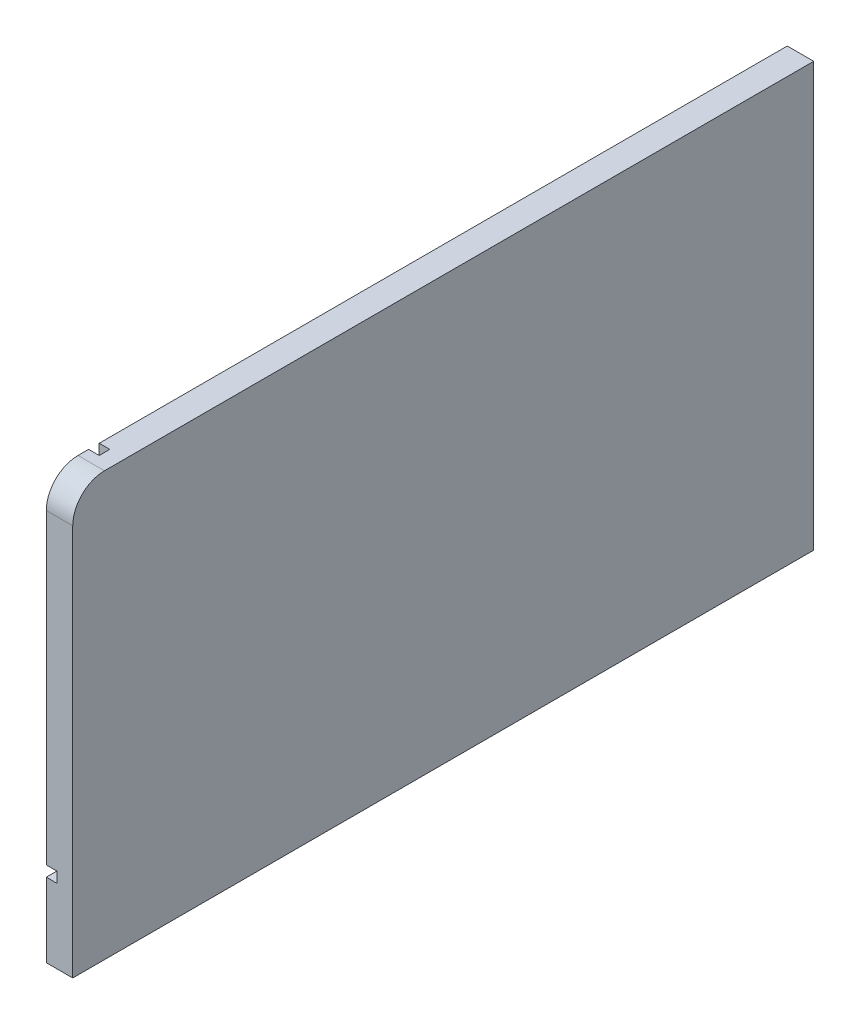
SolidWorks part; units mm, degrees
ref_plane "Front Plane" through (0, 0, 0) normal (0, 0, 1) x (1, 0, 0)
ref_plane "Top Plane" through (0, 0, 0) normal (0, 1, 0) x (1, 0, 0)
ref_plane "Right Plane" through (0, 0, 0) normal (1, 0, 0) x (0, 0, -1)
sketch "Sketch1" plane through (0, 0, 0) normal (1, 0, 0) x (0, 0, -1)
  line L1 (0, 0) -> (444.5, 0)
  line L2 (0, 0) -> (0, 234.95)
  line L3 (19.05, 254) -> (444.5, 254)
  line L4 (444.5, 0) -> (444.5, 254)
  arc A0 (0, 234.95) -> (19.05, 254) centre (19.05, 234.95) cw
  point P7 (444.5, 254)
  point P8 (0, 254)
  dimension "D3" = 19.05
  dimension "D1" = 444.5
  dimension "D2" = 254
extrude "Boss-Extrude1" add sketch "Sketch1" along normal blind 15.875
sketch "Sketch2" plane through (0, 0, -444.5) normal (0, 0, -1) x (-1, 0, 0)
  line L0 (0, 0) -> (0, 254) construction
  line L1 (0, 50.8) -> (-6.35, 50.8)
  line L2 (0, 50.8) -> (0, 44.45)
  line L3 (0, 44.45) -> (-6.35, 44.45)
  line L4 (-6.35, 50.8) -> (-6.35, 44.45)
  line L5 (-15.875, 254) -> (0, 254) construction
  dimension "D1" = 6.35
  dimension "D2" = 6.35
  dimension "D3" = 203.2
extrude "Cut-Extrude1" cut sketch "Sketch2" along direction (0, 0, 1) on the side against the normal through all
sketch "Sketch3" plane through (0, 0, 0) normal (0, -1, 0) x (1, 0, 0)
  line L0 (0, 0) -> (0, -444.5) construction
  line L1 (0, -6.35) -> (6.35, -6.35)
  line L2 (0, -6.35) -> (0, -12.7)
  line L3 (0, -12.7) -> (6.35, -12.7)
  line L4 (6.35, -6.35) -> (6.35, -12.7)
  line L5 (15.875, 0) -> (0, 0) construction
  dimension "D1" = 6.35
  dimension "D2" = 6.35
  dimension "D3" = 6.35
extrude "Cut-Extrude2" cut sketch "Sketch3" against normal up to next
sketch "Sketch4" plane through (0, 254, 0) normal (0, 1, 0) x (1, 0, 0)
  line L0 (0, 444.5) -> (0, 19.05) construction
  line L1 (0, 25.4) -> (6.35, 25.4)
  line L2 (0, 25.4) -> (0, 31.75)
  line L3 (0, 31.75) -> (6.35, 31.75)
  line L4 (6.35, 25.4) -> (6.35, 31.75)
  line L6 (15.875, 19.05) -> (0, 19.05) construction
  dimension "D1" = 6.35
  dimension "D2" = 6.35
  dimension "D3" = 6.35
extrude "Cut-Extrude3" cut sketch "Sketch4" against normal up to next
